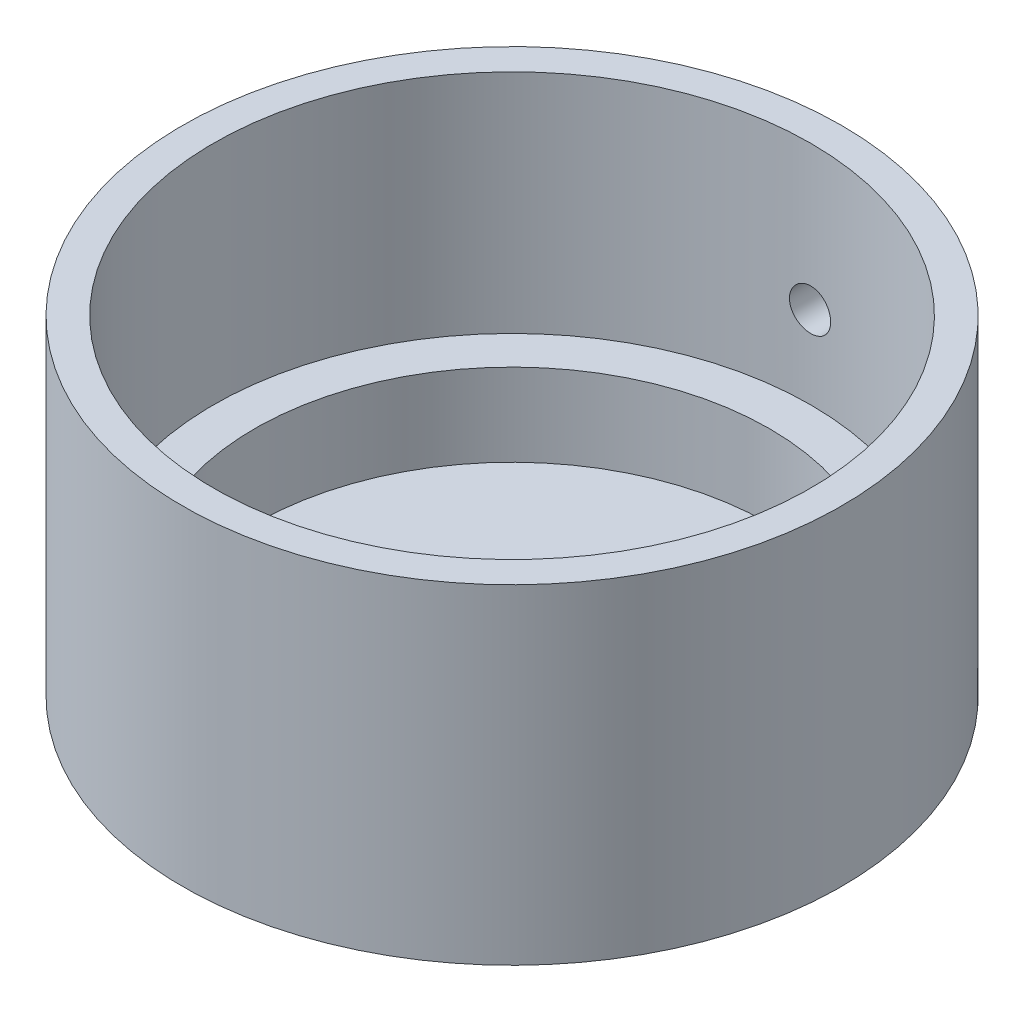
SolidWorks part; units mm, degrees
ref_plane "Спереди" through (0, 0, 0) normal (0, 0, 1) x (1, 0, 0)
ref_plane "Сверху" through (0, 0, 0) normal (0, 1, 0) x (1, 0, 0)
ref_plane "Справа" through (0, 0, 0) normal (1, 0, 0) x (0, 0, -1)
sketch "Эскиз1" plane through (0, 0, 0) normal (0, 0, 1) x (1, 0, 0)
  line L0 (0, 0) -> (12.5, 0)
  line L1 (12.5, 0) -> (12.5, 4)
  line L2 (12.5, 4) -> (14.5, 4)
  line L3 (14.5, 4) -> (14.5, 15)
  line L4 (14.5, 15) -> (16, 15)
  line L5 (16, 15) -> (16, -1)
  line L6 (16, -1) -> (0, -1)
  line L7 (0, -1) -> (0, 0)
  dimension "D1" = 1
  dimension "D2" = 12.5
  dimension "D3" = 14.5
  dimension "D4" = 1.5
  dimension "D5" = 4
  dimension "D6" = 11
revolve "Повернуть1" add sketch "Эскиз1" angle 360 about L7
sketch "Эскиз2" plane through (0, 0, 0) normal (0, 0, 1) x (1, 0, 0)
  line L0 (0, 0) -> (0, 8) construction
  circle A0 centre (0, 8) radius 1
  dimension "D1" = 2
  dimension "D2" = 8
extrude "Вырез-Вытянуть1" cut sketch "Эскиз2" against normal up to next
